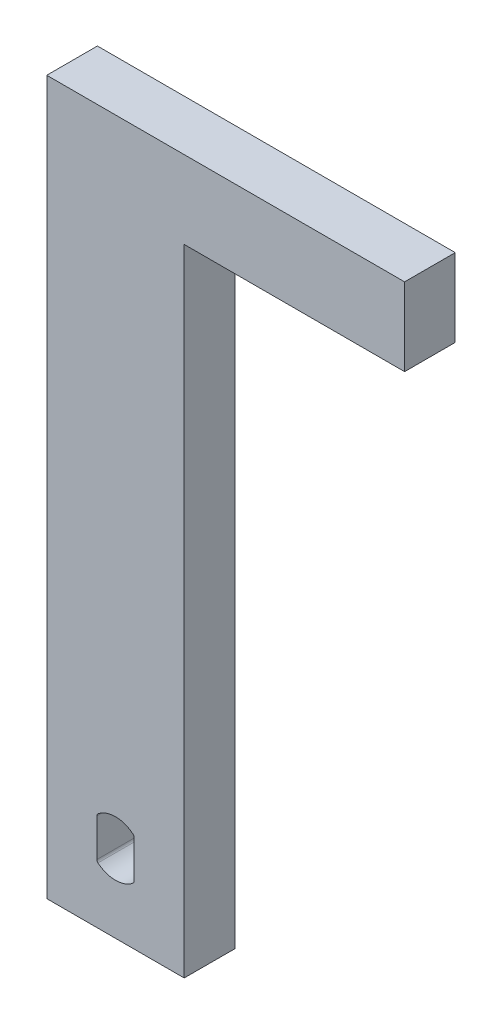
SolidWorks part; units mm, degrees
ref_plane "Front Plane" through (0, 0, 0) normal (0, 0, 1) x (1, 0, 0)
ref_plane "Top Plane" through (0, 0, 0) normal (0, 1, 0) x (1, 0, 0)
ref_plane "Right Plane" through (0, 0, 0) normal (1, 0, 0) x (0, 0, -1)
sketch "Sketch1" plane through (0, 0, 0) normal (0, 0, 1) x (1, 0, 0)
  line L1 (-6.731, 34.925) -> (6.731, 34.925)
  line L2 (-6.731, 34.925) -> (-6.731, -34.925)
  line L3 (-6.731, -34.925) -> (6.731, -34.925)
  line L4 (6.731, 34.925) -> (6.731, -34.925)
  line L5 (-6.731, 34.925) -> (6.731, -34.925) construction
  line L6 (-6.731, -34.925) -> (6.731, 34.925) construction
  point P0 (0, 0)
  dimension "D1" = 13.462
  dimension "D2" = 69.85
extrude "Boss-Extrude1" add sketch "Sketch1" along normal blind 4.9609
sketch "Sketch2" plane through (6.731, 0, 0) normal (1, 0, 0) x (0, 0, -1)
  line L0 (0, -34.925) -> (0, 34.925) construction
  line L1 (-4.9609, 34.925) -> (0, 34.925)
  line L2 (-4.9609, 34.925) -> (-4.9609, 27.305)
  line L3 (-4.9609, 27.305) -> (0, 27.305)
  line L4 (0, 34.925) -> (0, 27.305)
  dimension "D1" = 7.62
extrude "Boss-Extrude2" add sketch "Sketch2" along normal blind 21.59
sketch "Sketch3" plane through (0, 0, 4.9609) normal (0, 0, 1) x (1, 0, 0)
  line L0 (0, -27.3046) -> (0, -34.925) construction
  line L1 (0, -27.3046) -> (-1.825, -27.3046) construction
  line L2 (-1.825, -29.1578) -> (-1.825, -25.4514)
  line L3 (1.825, -25.4514) -> (1.825, -29.1578)
  line L4 (0, -27.3046) -> (1.825, -27.3046) construction
  line L6 (6.731, -34.925) -> (6.731, 27.305)
  line L7 (6.731, 27.305) -> (28.321, 27.305)
  line L8 (28.321, 27.305) -> (28.321, 34.925)
  line L9 (28.321, 34.925) -> (-6.731, 34.925)
  line L10 (-6.731, 34.925) -> (-6.731, -34.925)
  line L11 (-6.731, -34.925) -> (6.731, -34.925)
  line L12 (6.731, -34.925) -> (6.731, 27.305)
  line L13 (6.731, 27.305) -> (28.321, 27.305)
  line L14 (28.321, 27.305) -> (28.321, 34.925)
  line L15 (28.321, 34.925) -> (-6.731, 34.925)
  line L16 (-6.731, 34.925) -> (-6.731, -34.925)
  line L17 (-6.731, -34.925) -> (6.731, -34.925)
  line L19 (0, -24.6046) -> (0, -30.0046) construction
  arc A6 (-1.7156, -25.2197) -> (-1.825, -25.4514) centre (-1.525, -25.4514) ccw
  arc A7 (1.7156, -25.2197) -> (-1.7156, -25.2197) centre (0, -27.3046) ccw
  arc A8 (1.825, -25.4514) -> (1.7156, -25.2197) centre (1.525, -25.4514) ccw
  arc A9 (1.7156, -29.3894) -> (1.825, -29.1578) centre (1.525, -29.1578) ccw
  arc A10 (-1.7156, -29.3894) -> (1.7156, -29.3894) centre (0, -27.3046) ccw
  arc A11 (-1.825, -29.1578) -> (-1.7156, -29.3894) centre (-1.525, -29.1578) ccw
  dimension "D4" = 2.7
  dimension "D5" = 0.3
  dimension "D6" = 0.2562
  dimension "D7" = 1.825
  dimension "D2" = 90
  dimension "D3" = 3.7064
  dimension "D1" = 0
extrude "Cut-Extrude1" cut sketch "Sketch3" against normal through all flip side to cut
